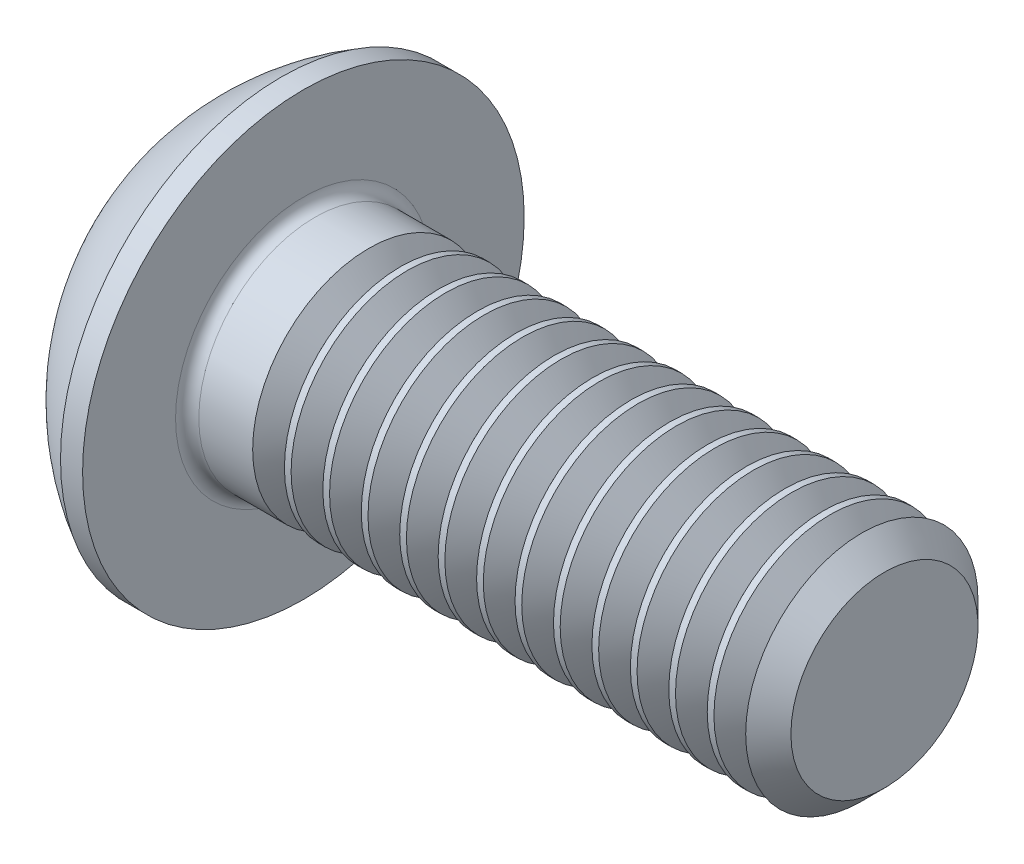
SolidWorks part; units mm, degrees
material "AISI 1045 Aço, trefilado"
ref_plane "Plane1" through (0, 0, 0) normal (0, 0, 1) x (1, 0, 0)
ref_plane "Plane2" through (0, 0, 0) normal (0, 1, 0) x (1, 0, 0)
ref_plane "Plane3" through (0, 0, 0) normal (1, 0, 0) x (0, 0, -1)
sketch "BodySke" plane through (0, 0, 0) normal (0, 0, 1) x (1, 0, 0)
  line L0 (12.2, 0) -> (12.2, 1.61)
  line L1 (11.81, 2) -> (2.2, 2)
  line L2 (2.2, 2) -> (2.2, 3.8)
  line L3 (2.2, 3.8) -> (1.82, 3.8)
  line L4 (0, 0) -> (101.6, 0) construction
  line L5 (2.2, -3.8) -> (1.82, -3.8) construction
  line L6 (55.6768, -2) -> (2.2, -2) construction
  line L7 (12.2, 0) -> (0, 0)
  line L8 (0, 1.9) -> (0, -1.9) construction
  line L9 (0, 0) -> (0, 1.9)
  line L10 (12.2, 1.61) -> (11.81, 2)
  line L11 (12.2, -1.61) -> (11.81, -2) construction
  line L12 (2.9, 9.525) -> (2.9, -2) construction
  line L13 (2.2, 9.525) -> (2.2, -2) construction
  arc A1 (0, 1.9) -> (1.82, 3.8) centre (3.8853, 0) cw
  dimension "D1" = 3.8
  dimension "Diameter" = 4
  dimension "Length" = 10
  dimension "Head_dia" = 7.6
  dimension "Head_ht" = 2.2
  dimension "Head_side_ht" = 0.38
  dimension "Minor_dia" = 3.22
  dimension "Body_ch_ang" = 45
  dimension "Advance" = 0.7
  dimension "Thread_nom" = 10
revolve "BaseBody" add sketch "BodySke" angle 360 about L4
cosmetic thread "ThreadCosmetic" [suppressed] parameters "Thread_length"=8.6, "Thread_minor"=3.22
fillet "Fillet1" radius 0.2 1 edges at (2.2, 0, 2)
sketch "Sketch2" plane through (0, 0, 0) normal (0, 0, 1) x (1, 0, 0)
  line L0 (0, 1.25) -> (1.3, 1.25)
  line L1 (1.3, 1.25) -> (2.0217, 0)
  line L3 (2.0217, 0) -> (0, 0)
  line L4 (0, 0) -> (0, 1.25)
  line L5 (0, -1.25) -> (1.3, -1.25) construction
  line L6 (0, 0) -> (47.625, 0) construction
  dimension "D2" = 60
  dimension "PreBroach_depth" = 1.3
  dimension "PreBroach_dia" = 2.5
revolve "PreBroach" cut sketch "Sketch2" angle 360 about L6
sketch "Sketch3" plane through (0, 0, 0) normal (1, 0, 0) x (0, 0, -1)
  line L0 (-1.25, -0.7217) -> (-1.25, 0.7217)
  line L1 (-1.25, 0.7217) -> (0, 1.4434)
  line L2 (0, 1.4434) -> (1.25, 0.7217)
  line L3 (1.25, 0.7217) -> (1.25, -0.7217)
  line L4 (1.25, -0.7217) -> (0, -1.4434)
  line L5 (0, -1.4434) -> (-1.25, -0.7217)
  dimension "D1" = 1.25
  dimension "D2" = 1.25
  dimension "D3" = 2.5
  dimension "Hex_size" = 2.5
extrude "Hex" cut sketch "Sketch3" along normal blind 1.3
sketch "ThdSchSke" plane through (0, 0, 0) normal (0, 0, 1) x (1, 0, 0)
  line L0 (3.6, -1.61) -> (3.3269, -2)
  line L1 (3.6, -1.61) -> (3.8731, -2)
  line L2 (3.8731, -2) -> (3.8731, -2.5)
  line L3 (-3.175, 0) -> (5.1513, 0) construction
  line L5 (3.8731, -2.5) -> (3.3269, -2.5)
  line L6 (3.3269, -2.5) -> (3.3269, -2)
  dimension "Thread_minor" = 3.22
  dimension "Diameter" = 4
  dimension "Start" = 3.6
  dimension "SideAngle" = 55
  dimension "VeeAngle" = 70
  dimension "Overcut" = 5
revolve "ThreadSchematic" cut sketch "ThdSchSke" angle 360 about L3
pattern_linear "ThdSchPat" count 13 spacing 0.6615 along (1, 0, 0) of "ThreadSchematic"
equation "\"D1@BodySke\" = \"Head_dia@BodySke\" * .5"
equation "\"Thread_minor@ThreadCosmetic\" = \"Minor_dia@BodySke\""
equation "\"D1@Sketch3\" = \"Hex_size@Sketch3\" / 2"
equation "\"D2@Sketch3\" = \"D1@Sketch3\""
equation "\"D3@Sketch3\" = \"Hex_size@Sketch3\""
equation "\"Thread_length@ThreadCosmetic\" = ((sgn( (\"Length@BodySke\" - \"Advance@BodySke\" * 2.0) - \"Thread_nom@BodySke\" )-1)*( (\"Length@BodySke\" - \"Advance@BodySke\" * 2.0) - \"Thread_nom@BodySke\" ))/-2+ \"Thread_nom@BodySke\""
equation "\"Thread_minor@ThdSchSke\" = \"Minor_dia@BodySke\""
equation "\"Diameter@ThdSchSke\" = \"Diameter@BodySke\""
equation "\"Overcut@ThdSchSke\" = \"Diameter@BodySke\" * 1.25"
equation "\"Start@ThdSchSke\" = \"Head_ht@BodySke\" + \"Length@BodySke\" - \"Thread_length@ThreadCosmetic\"  '---Non-countersunk---"
equation "\"Num_threads@ThdSchPat\" = int( \"Thread_length@ThreadCosmetic\" / \"Advance@BodySke\" + 0.999 )  + 1"
equation "\"Advance@ThdSchPat\" = \"Thread_length@ThreadCosmetic\" /  (\"Num_threads@ThdSchPat\" - 1) 'relax it"
equation "\"Num_threads@ThdSchPat\" = \"Num_threads@ThdSchPat\" - sgn( \"Num_threads@ThdSchPat\" - 1) '---chamfered tips only---"
